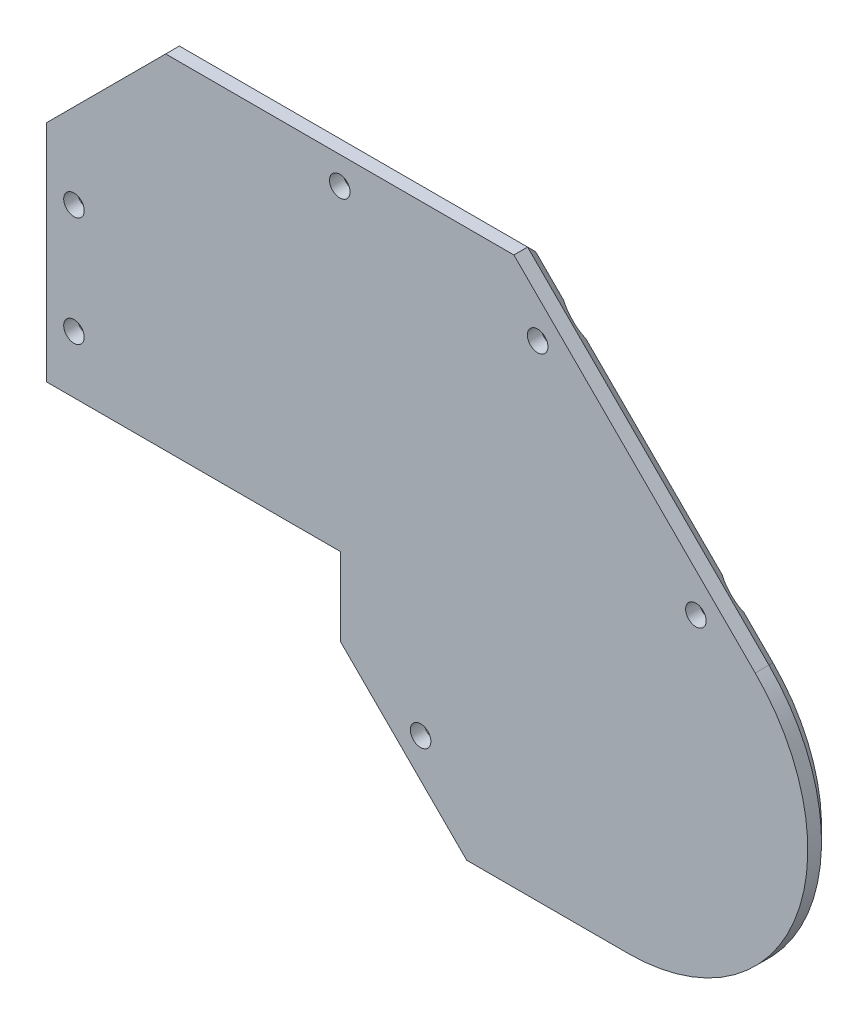
SolidWorks part; units mm, degrees
ref_plane "Plano frontal" through (0, 0, 0) normal (0, 0, 1) x (1, 0, 0)
ref_plane "Plano superior" through (0, 0, 0) normal (0, 1, 0) x (1, 0, 0)
ref_plane "Plano direito" through (0, 0, 0) normal (1, 0, 0) x (0, 0, -1)
sketch "Model" plane through (0, 0, 0) normal (0, 0, 1) x (1, 0, 0)
  line L0 (0, 0) -> (39, 0) construction
  line L1 (-0.7, 2.5) -> (39, 2.5)
  line L2 (39.7, 0) -> (39.7, -6.8548) construction
  line L3 (0, 0) -> (0, 31.4419) construction
  line L4 (50.1111, 46.949) -> (15.5071, 46.949) construction
  line L5 (0, 31.4419) -> (15.5071, 46.949) construction
  line L6 (42.2, -9.3548) -> (52.4452, -19.6) construction
  line L7 (39, -7.1448) -> (51.9502, -20.095) construction
  line L8 (97.9635, 12.6635) -> (63.6779, 46.949) construction
  line L9 (50.1111, 46.949) -> (63.6779, 46.949) construction
  line L10 (52.4452, -19.6) -> (59.4452, -26.6) construction
  line L11 (81.7, -26.6) -> (59.4452, -26.6) construction
  line L12 (-0.7, 0) -> (39, 0)
  line L13 (-0.7, 0) -> (-3.2, 0)
  line L14 (42.2, -10.3448) -> (51.9502, -20.095)
  line L15 (51.9502, -20.095) -> (59.1552, -27.3)
  line L16 (81.7, -27.3) -> (59.1552, -27.3)
  line L17 (98.4584, 13.1584) -> (63.9678, 47.649)
  line L18 (50.1111, 47.649) -> (63.9678, 47.649)
  line L19 (50.1111, 47.649) -> (15.2171, 47.649)
  line L20 (-0.7, 31.7319) -> (15.2171, 47.649)
  line L21 (-0.7, 2.5) -> (-0.7, 31.7319)
  line L22 (0, 0) -> (-0.7, 0) construction
  line L23 (38.8515, -10.5318) -> (50.1824, -21.8627) construction
  line L24 (-3.2, 0) -> (-3.2, 5)
  line L25 (-0.7, -0.7) -> (-0.7, 31.7319) construction
  line L26 (-0.7, -0.7) -> (39, -0.7) construction
  line L27 (39, -0.7) -> (39, -7.1448) construction
  line L28 (39, -0.7) -> (39, -0.7) construction
  line L29 (39, 0) -> (39.7, 0)
  line L30 (39.7, 0) -> (39.7, -11.3803)
  line L31 (39, 2.5) -> (39.7, 2.5)
  line L32 (39.7, 2.5) -> (42.2, 2.5)
  line L33 (39, 0) -> (39.7, 0) construction
  line L34 (42.2, 2.5) -> (42.2, -10.3448)
  line L35 (-3.2, 5) -> (-3.2, 32.7674)
  line L36 (-3.2, 32.7674) -> (14.1816, 50.149)
  line L37 (50.1111, 50.149) -> (14.1816, 50.149)
  line L38 (50.1111, 50.149) -> (65.0034, 50.149)
  line L39 (100.2262, 14.9262) -> (65.0034, 50.149)
  line L40 (81.7, -29.8) -> (58.1197, -29.8)
  line L41 (50.1824, -21.8627) -> (58.1197, -29.8)
  line L42 (39.7, -11.3803) -> (50.1824, -21.8627)
  line L43 (-0.7, 2.5) -> (-5.7, 2.5) construction
  line L44 (-5.7, 0) -> (-5.7, 2.5) construction
  line L45 (-0.7, 0) -> (-5.7, 0) construction
  line L46 (-3.2, 5) -> (-8.2, 5) construction
  line L47 (-8.2, -2.5) -> (-8.2, 5) construction
  line L48 (-0.7, -2.5) -> (39, -2.5) construction
  line L49 (-0.7, -2.5) -> (-8.2, -2.5) construction
  line L51 (40.6192, -8.764) -> (51.9502, -20.095) construction
  line L52 (39.7, -6.8548) -> (52.4452, -19.6) construction
  arc A0 (81.7, -27.3) -> (98.4584, 13.1584) centre (81.7, -3.6) ccw
  arc A1 (81.7, -29.8) -> (100.2262, 14.9262) centre (81.7, -3.6) ccw
  circle A2 centre (59.0726, 19.0274) radius 7.35 construction
  arc A5 (81.7, -26.6) -> (97.9635, 12.6635) centre (81.7, -3.6) ccw construction
  circle A6 centre (81.7, -3.6) radius 7.3 construction
  circle A13 centre (27.384, 23.481) radius 7.35 construction
  dimension "D2" = 2.5
  dimension "D1" = 0.7
extrude "Ressalto-extrusão1" add sketch "Model" along normal blind 48
sketch "Esboço12" plane through (57.5762, 57.5762, 0) normal (0.7071, 0.7071, 0) x (0, 0, -1)
  line L0 (-48, -35.4099) -> (-44, -35.4099) construction
  line L1 (-48, -60.3162) -> (-48, -10.5036) construction
  line L2 (-44, -35.4099) -> (-44, -43.4099) construction
  line L3 (-44, -35.4099) -> (-44, -19.4099) construction
  line L4 (-44, -19.4099) -> (-44, -51.4099) construction
  circle A0 centre (-44, -19.4099) radius 1.5
  circle A1 centre (-44, -51.4099) radius 1.5
extrude "Corte-extrusão10" cut sketch "Esboço12" against normal blind 10
sketch "Esboço13" plane through (0, 50.149, 0) normal (0, 1, 0) x (1, 0, 0)
  line L0 (39.5925, -48) -> (39.5925, -44) construction
  line L1 (65.0034, -48) -> (14.1816, -48) construction
  circle A0 centre (39.5925, -44) radius 1.5
extrude "Corte-extrusão11" cut sketch "Esboço13" against normal blind 10
sketch "Esboço14" plane through (-3.2, 0, 0) normal (-1, 0, 0) x (0, 0, 1)
  line L0 (48, 16.3837) -> (44, 16.3837) construction
  line L1 (48, 32.7674) -> (48, 0) construction
  line L2 (44, 16.3837) -> (44, 24.3837) construction
  line L3 (44, 24.3837) -> (44, 8.3837) construction
  circle A0 centre (44, 24.3837) radius 1.5
  circle A1 centre (44, 8.3837) radius 1.5
extrude "Corte-extrusão12" cut sketch "Esboço14" against normal blind 10
sketch "Esboço15" plane through (14.1598, 14.1598, 0) normal (-0.7071, -0.7071, 0) x (0, 0, 1)
  line L0 (48, -62.1686) -> (44, -62.1686) construction
  line L1 (48, -62.1686) -> (0, -62.1686) construction
  line L2 (0, -36.4548) -> (0, -50.9436) construction
  line L3 (0, -50.9436) -> (0, -60.8431) construction
  line L4 (0, -36.4548) -> (0, -50.9436) construction
  line L5 (0, -50.9436) -> (0, -60.8431) construction
  line L6 (0, -60.8431) -> (0, -36.4548) construction
  line L7 (0, -36.4548) -> (0, -48.6489) construction
  line L8 (0, -48.6489) -> (48, -48.6489) construction
  line L9 (48, -36.1192) -> (48, -62.1686) construction
  line L10 (48, -48.6489) -> (44, -48.6489) construction
  circle A0 centre (44, -48.6489) radius 1.5
extrude "Corte-extrusão13" cut sketch "Esboço15" against normal blind 10
sketch "Esboço16" plane through (0, 0, 48) normal (0, 0, 1) x (1, 0, 0)
  line L0 (39.7, 0) -> (39.7, -2)
  line L4 (42.2, -2) -> (42.2, 2.5)
  line L5 (42.2, 2.5) -> (-0.7, 2.5)
  line L6 (39.7, 0) -> (39.7, -2) construction
  line L8 (39.7, -2) -> (42.2, -2)
  line L12 (-0.7, 0) -> (39.7, 0)
  line L13 (-0.7, 2.5) -> (-0.7, 0)
extrude "Corte-extrusão14" cut sketch "Esboço16" against normal blind 10
sketch "Esboço17" plane through (0, 0, 0) normal (0, 0, -1) x (-1, 0, 0)
  line L0 (-92.8678, 22.2846) -> (-94.9892, 20.1632) construction
  line L1 (-92.8678, 22.2846) -> (-94.9892, 20.1632) construction
  line L2 (-70.2404, 44.912) -> (-72.3617, 42.7907) construction
  line L3 (-70.2404, 44.912) -> (-72.3617, 42.7907) construction
  line L4 (-38.0925, 50.149) -> (-41.0925, 50.149) construction
  line L5 (-38.0925, 50.149) -> (-41.0925, 50.149) construction
  line L6 (3.2, 22.8837) -> (3.2, 25.8837) construction
  line L7 (3.2, 22.8837) -> (3.2, 25.8837) construction
  line L8 (3.2, 6.8837) -> (3.2, 9.8837) construction
  line L9 (3.2, 6.8837) -> (3.2, 9.8837) construction
  line L10 (-49.6205, -21.3008) -> (-47.4992, -19.1795) construction
  line L11 (-49.6205, -21.3008) -> (-47.4992, -19.1795) construction
  line L12 (-93.9285, 21.2239) -> (-91.1001, 18.3955) construction
  line L13 (-71.3011, 43.8513) -> (-68.4727, 41.0229) construction
  line L14 (-39.5925, 50.149) -> (-39.5925, 46.149) construction
  line L15 (3.2, 24.3837) -> (-0.8, 24.3837) construction
  line L16 (3.2, 8.3837) -> (-0.8, 8.3837) construction
  line L17 (-48.5598, -20.2402) -> (-51.3883, -17.4117) construction
  line L18 (-69.8727, 39.6229) -> (-67.0727, 39.6229)
  line L19 (-92.5001, 19.7955) -> (-89.7001, 19.7955)
  line L20 (-92.5001, 19.7955) -> (-92.5001, 16.9955)
  line L21 (-92.5001, 16.9955) -> (-89.7001, 16.9955)
  line L22 (-89.7001, 19.7955) -> (-89.7001, 16.9955)
  line L23 (-92.5001, 19.7955) -> (-89.7001, 16.9955) construction
  line L24 (-92.5001, 16.9955) -> (-89.7001, 19.7955) construction
  line L25 (-69.8727, 39.6229) -> (-67.0727, 42.4229) construction
  line L26 (-69.8727, 42.4229) -> (-67.0727, 39.6229) construction
  line L27 (-69.8727, 42.4229) -> (-69.8727, 39.6229)
  line L28 (-69.8727, 42.4229) -> (-67.0727, 42.4229)
  line L29 (-67.0727, 42.4229) -> (-67.0727, 39.6229)
  line L30 (-38.1925, 47.549) -> (-38.1925, 44.749)
  line L31 (-40.9925, 44.749) -> (-38.1925, 47.549) construction
  line L32 (-40.9925, 47.549) -> (-40.9925, 44.749)
  line L33 (-40.9925, 47.549) -> (-38.1925, 44.749) construction
  line L34 (-40.9925, 44.749) -> (-38.1925, 44.749)
  line L35 (-40.9925, 47.549) -> (-38.1925, 47.549)
  line L36 (-2.2, 25.7837) -> (0.6, 22.9837) construction
  line L37 (-2.2, 22.9837) -> (0.6, 22.9837)
  line L38 (0.6, 25.7837) -> (0.6, 22.9837)
  line L39 (-2.2, 25.7837) -> (0.6, 25.7837)
  line L40 (-2.2, 22.9837) -> (0.6, 25.7837) construction
  line L41 (-2.2, 25.7837) -> (-2.2, 22.9837)
  line L42 (0.6, 9.7837) -> (0.6, 6.9837)
  line L43 (-2.2, 9.7837) -> (0.6, 9.7837)
  line L44 (-2.2, 6.9837) -> (0.6, 6.9837)
  line L45 (-2.2, 9.7837) -> (0.6, 6.9837) construction
  line L46 (-2.2, 9.7837) -> (-2.2, 6.9837)
  line L47 (-2.2, 6.9837) -> (0.6, 9.7837) construction
  line L48 (-52.7883, -18.8117) -> (-49.9883, -18.8117)
  line L49 (-52.7883, -16.0117) -> (-49.9883, -18.8117) construction
  line L50 (-52.7883, -18.8117) -> (-49.9883, -16.0117) construction
  line L51 (-52.7883, -16.0117) -> (-49.9883, -16.0117)
  line L52 (-49.9883, -16.0117) -> (-49.9883, -18.8117)
  line L53 (-52.7883, -16.0117) -> (-52.7883, -18.8117)
  circle A0 centre (-91.1001, 18.3955) radius 4
  circle A1 centre (-68.4727, 41.0229) radius 4
  circle A2 centre (-39.5925, 46.149) radius 4
  circle A3 centre (-0.8, 24.3837) radius 4
  circle A4 centre (-0.8, 8.3837) radius 4
  circle A5 centre (-51.3883, -17.4117) radius 4
extrude "Ressalto-extrusão2" add sketch "Esboço17" against normal blind 4
sketch "Esboço18" plane through (0, 0, 0) normal (0, 0, -1) x (-1, 0, 0)
  line L0 (-65.0034, 50.149) -> (-14.1816, 50.149) construction
  line L1 (-100.2262, 14.9262) -> (-65.0034, 50.149) construction
  line L2 (-14.1816, 50.149) -> (3.2, 32.7674) construction
  line L3 (3.2, 32.7674) -> (3.2, 0) construction
  line L4 (3.2, 0) -> (-39.7, 0) construction
  line L5 (-39.7, 0) -> (-39.7, -11.3803) construction
  line L6 (-39.7, -11.3803) -> (-58.1197, -29.8) construction
  line L7 (-58.1197, -29.8) -> (-81.7, -29.8) construction
  line L8 (-65.0034, 50.149) -> (-14.1816, 50.149)
  line L9 (-100.2262, 14.9262) -> (-65.0034, 50.149)
  line L10 (-14.1816, 50.149) -> (3.2, 32.7674)
  line L11 (3.2, 32.7674) -> (3.2, 0)
  line L12 (3.2, 0) -> (-39.7, 0)
  line L13 (-39.7, 0) -> (-39.7, -11.3803)
  line L14 (-39.7, -11.3803) -> (-58.1197, -29.8)
  line L15 (-58.1197, -29.8) -> (-81.7, -29.8)
  line L16 (-90.1687, 16.5268) -> (-90.1687, 19.3268) construction
  line L17 (-90.1687, 19.3268) -> (-92.29, 19.3268) construction
  line L18 (-90.1687, 16.5268) -> (-90.1687, 19.3268) construction
  line L19 (-90.1687, 19.3268) -> (-92.29, 19.3268) construction
  line L20 (-90.1687, 16.5268) -> (-92.6294, 18.9875) construction
  line L21 (-92.9687, 18.6482) -> (-92.29, 19.3268) construction
  line L22 (-90.1687, 19.3268) -> (-92.9687, 16.5268) construction
  arc A0 (-100.2262, 14.9262) -> (-81.7, -29.8) centre (-81.7, -3.6) ccw construction
  arc A1 (-100.2262, 14.9262) -> (-81.7, -29.8) centre (-81.7, -3.6) ccw
  circle A2 centre (-91.5687, 17.9268) radius 1.5
  circle A3 centre (-68.4727, 41.0229) radius 1.5
  circle A4 centre (-39.5925, 46.149) radius 1.5
  circle A5 centre (-0.8, 24.3837) radius 1.5
  circle A6 centre (-51.3883, -17.4117) radius 1.5
  circle A7 centre (-0.8, 8.3837) radius 1.5
extrude "Ressalto-extrusão3" add sketch "Esboço18" along normal blind 4
chamfer "Chanfro1" distance 2 angle 45 9 edges at (39.5925, 50.149, -4) (5.4908, 41.4582, -4) (-3.2, 16.3837, -4) (18.25, 0, -4) (39.7, -5.6902, -4) (48.9098, -20.5902, -4) (69.9098, -29.8, -4) (105.9056, -13.6263, -4) (82.6148, 32.5376, -4)
sketch "Esboço19" plane through (0, 0, 48) normal (0, 0, 1) x (1, 0, 0)
  line L8 (65.0034, 50.149) -> (14.1816, 50.149)
  line L9 (14.1816, 50.149) -> (-3.2, 32.7674)
  line L10 (-3.2, 32.7674) -> (-3.2, 0)
  line L11 (-3.2, 0) -> (39.7, 0)
  line L12 (39.7, 0) -> (39.7, -11.3803)
  line L13 (39.7, -11.3803) -> (58.1197, -29.8)
  line L14 (58.1197, -29.8) -> (81.7, -29.8)
  line L15 (100.2262, 14.9262) -> (65.0034, 50.149)
  line L16 (65.0034, 50.149) -> (14.1816, 50.149)
  line L17 (14.1816, 50.149) -> (-3.2, 32.7674)
  line L18 (-3.2, 32.7674) -> (-3.2, 0)
  line L19 (-3.2, 0) -> (39.7, 0)
  line L20 (39.7, 0) -> (39.7, -11.3803)
  line L21 (39.7, -11.3803) -> (58.1197, -29.8)
  line L22 (58.1197, -29.8) -> (81.7, -29.8)
  line L23 (100.2262, 14.9262) -> (65.0034, 50.149)
  arc A5 (81.7, -29.8) -> (100.2262, 14.9262) centre (81.7, -3.6) ccw
  arc A6 (81.7, -29.8) -> (100.2262, 14.9262) centre (81.7, -3.6) ccw
  dimension "D3" = 0
extrude "Corte-extrusão15" cut sketch "Esboço19" against normal up to surface (48 mm away) up to face at (43.9312, 14.8678, 0)
sketch "Esboço20" plane through (0, 0, -4) normal (0, 0, -1) x (-1, 0, 0)
  circle A0 centre (-0.8, 24.3837) radius 3
  circle A1 centre (-0.8, 8.3837) radius 3
  circle A2 centre (-39.5925, 46.149) radius 3
  circle A3 centre (-68.4727, 41.0229) radius 3
  circle A4 centre (-51.3883, -17.4117) radius 3
  circle A5 centre (-91.5687, 17.9268) radius 3
extrude "Corte-extrusão16" cut sketch "Esboço20" against normal blind 2
